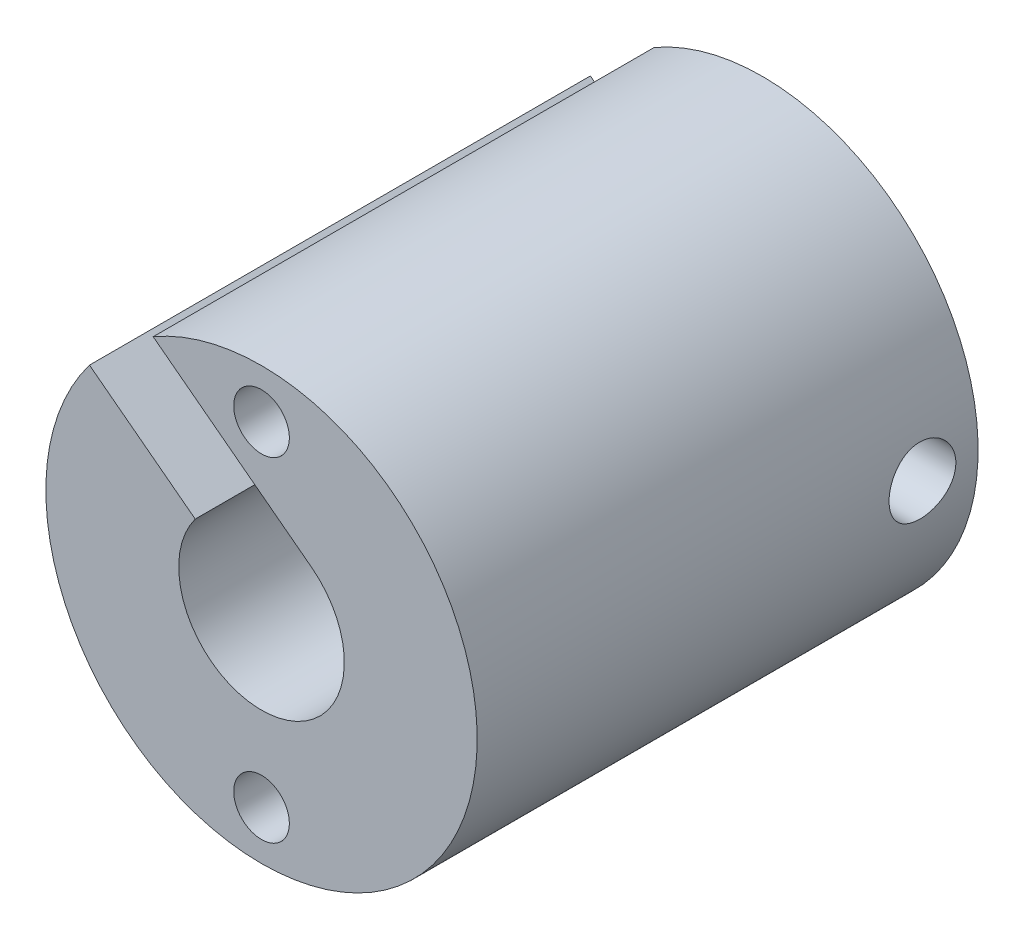
SolidWorks part; units mm, degrees
material "6061-T6 (SS)"
ref_plane "前视基准面" through (0, 0, 0) normal (0, 0, 1) x (1, 0, 0)
ref_plane "上视基准面" through (0, 0, 0) normal (0, 1, 0) x (1, 0, 0)
ref_plane "右视基准面" through (0, 0, 0) normal (1, 0, 0) x (0, 0, -1)
sketch "草图1" plane through (0, 0, 0) normal (0, 0, 1) x (1, 0, 0)
  circle A0 centre (0, 0) radius 2.975
  circle A1 centre (0, 0) radius 7.75
  circle A2 centre (0, 0) radius 6 construction
  circle A3 centre (0, 6) radius 1
  circle A4 centre (0, -6) radius 1
  point P11 (0, 0)
  dimension "D1" = 5.95
  dimension "D2" = 15.5
  dimension "D3" = 12
  dimension "D4" = 2
  dimension "D5" = 2
extrude "凸台-拉伸1" add sketch "草图1" along normal blind 18
cosmetic thread "装饰螺纹线1" parameters "D1"=5, "D2"=2.5
cosmetic thread "装饰螺纹线2" parameters "D1"=5, "D2"=2.5
sketch "草图2" plane through (0, 0, 0) normal (1, 0, 0) x (0, 0, -1)
  line L0 (0, 0) -> (-2, 0) construction
  circle A0 centre (-2, 0) radius 1.2
  dimension "D2" = 2.4
  dimension "D1" = 2
extrude "切除-拉伸1" cut sketch "草图2" against normal through all both and the other way through all
cosmetic thread "装饰螺纹线3" parameters "D2"=3
cosmetic thread "装饰螺纹线4" parameters "D2"=3
sketch "草图3" plane through (0, 0, 0) normal (0, 0, -1) x (-1, 0, 0)
  line L4 (-1.8014, 2.3676) -> (3.8938, 6.7008)
  line L5 (3.8938, 6.7008) -> (6.1828, 6.7008)
  line L6 (6.1828, 6.7008) -> (6.1828, 4.6728)
  line L7 (6.1828, 4.6728) -> (2.3827, 1.7814)
  line L8 (2.3827, 1.7814) -> (-1.8014, 2.3676)
  circle A2 centre (0, 0) radius 2.975 construction
  circle A3 centre (0, 0) radius 7.75 construction
  circle A4 centre (0, 6) radius 1 construction
  dimension "D1" = 1.8
  dimension "D3" = 3
extrude "切除-拉伸2" cut sketch "草图3" against normal through all
